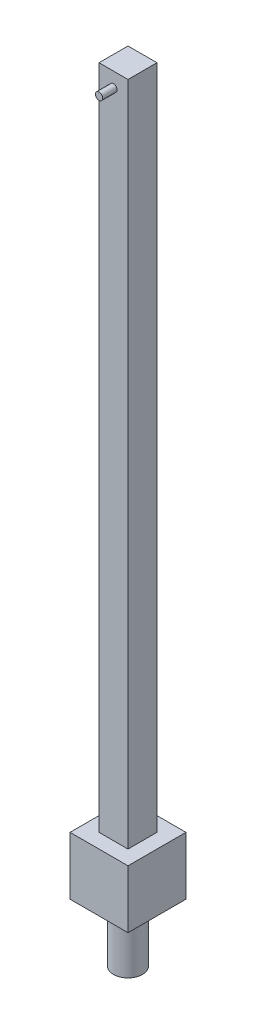
SolidWorks part; units mm, degrees
ref_plane "Front Plane" through (0, 0, 0) normal (0, 0, 1) x (1, 0, 0)
ref_plane "Top Plane" through (0, 0, 0) normal (0, 1, 0) x (1, 0, 0)
ref_plane "Right Plane" through (0, 0, 0) normal (1, 0, 0) x (0, 0, -1)
sketch "Sketch1" plane through (0, 0, 0) normal (0, 1, 0) x (1, 0, 0)
  line L1 (-10, 10) -> (10, 10)
  line L2 (-10, 10) -> (-10, -10)
  line L3 (-10, -10) -> (10, -10)
  line L4 (10, 10) -> (10, -10)
  line L5 (-10, 10) -> (10, -10) construction
  line L6 (-10, -10) -> (10, 10) construction
  point P0 (0, 0)
  dimension "D1" = 20
extrude "Boss-Extrude1" add sketch "Sketch1" along normal blind 500 contours L2 L3 L4 L1
sketch "Sketch2" plane through (0, 0, 0) normal (0, -1, 0) x (1, 0, 0)
  line L1 (-20, 20) -> (20, 20)
  line L2 (-20, 20) -> (-20, -20)
  line L3 (-20, -20) -> (20, -20)
  line L4 (20, 20) -> (20, -20)
  line L5 (-20, 20) -> (20, -20) construction
  line L6 (-20, -20) -> (20, 20) construction
  point P0 (0, 0)
  dimension "D1" = 40
extrude "Boss-Extrude2" add sketch "Sketch2" against normal blind 40
sketch "Sketch3" plane through (0, 0, 0) normal (0, -1, 0) x (1, 0, 0)
  circle A0 centre (0, 0) radius 10
  dimension "D1" = 20
extrude "Boss-Extrude3" add sketch "Sketch3" along normal blind 40
sketch "Sketch4" plane through (0, 0, 10) normal (0, 0, 1) x (1, 0, 0)
  line L0 (-10, 500) -> (10, 500) construction
  circle A0 centre (0, 490) radius 2.5
  dimension "D1" = 5
  dimension "D2" = 10
extrude "Boss-Extrude4" add sketch "Sketch4" along normal blind 10
